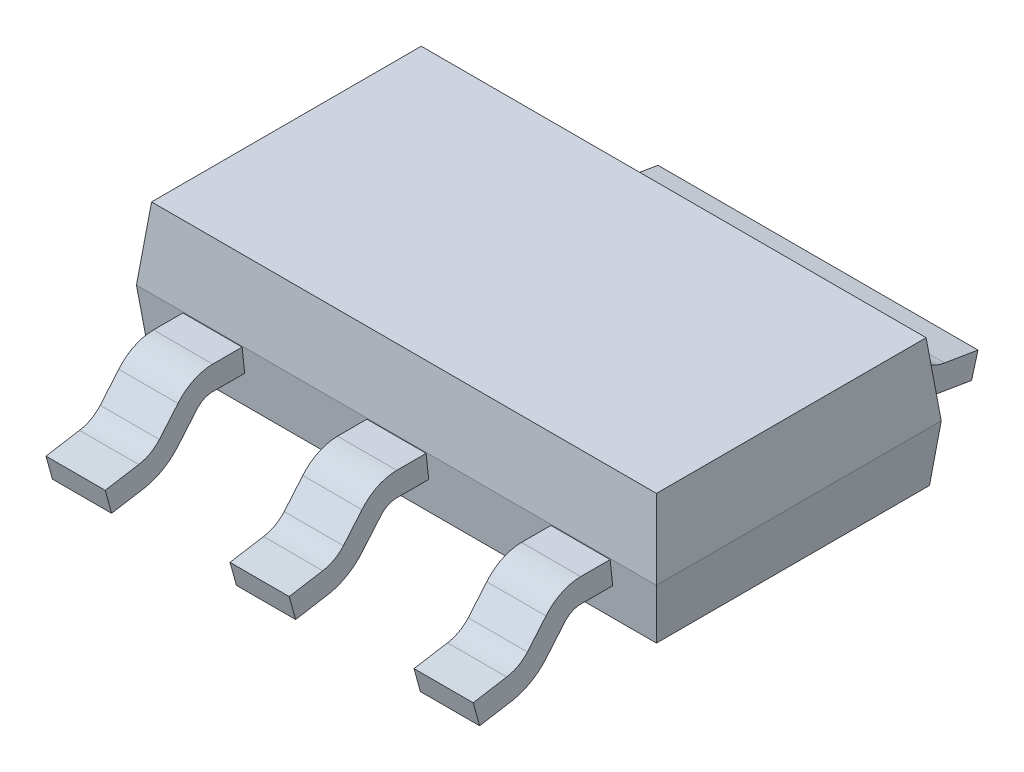
SolidWorks part; units mm, degrees
ref_plane "Plano frontal" through (0, 0, 0) normal (0, 0, 1) x (1, 0, 0)
ref_plane "Plano superior" through (0, 0, 0) normal (0, 1, 0) x (1, 0, 0)
ref_plane "Plano direito" through (0, 0, 0) normal (1, 0, 0) x (0, 0, -1)
sketch "Esboço1" plane through (0, 0, 0) normal (0, 1, 0) x (1, 0, 0)
  line L1 (-3.25, 1.78) -> (3.25, 1.78)
  line L2 (-3.25, 1.78) -> (-3.25, -1.78)
  line L3 (-3.25, -1.78) -> (3.25, -1.78)
  line L4 (3.25, 1.78) -> (3.25, -1.78)
  dimension "D1" = 3.25
  dimension "D2" = 6.5
  dimension "D3" = 1.78
  dimension "D4" = 3.56
extrude "Extrusão1" add sketch "Esboço1" along normal blind 0.9 draft 6 and the other way blind 0.7 draft 6
sketch "Esboço2" plane through (0, 0, 0) normal (1, 0, 0) x (0, 0, -1)
  line L0 (-1.7711, -0.0848) -> (-2.1389, -0.0848)
  line L1 (-1.7064, -0.7) -> (-1.78, 0) construction
  line L2 (-2.5209, -0.2622) -> (-2.7525, -0.5365)
  line L3 (-3.0523, -0.707) -> (-3.4711, -0.7768)
  arc A0 (-2.1389, -0.0848) -> (-2.5209, -0.2622) centre (-2.1389, -0.5848) ccw
  arc A1 (-2.7525, -0.5365) -> (-3.0523, -0.707) centre (-3.1345, -0.2138) cw
  point P8 (-2.3711, -0.0848)
  point P11 (-2.8711, -0.6768)
  dimension "D5" = 0.5
  dimension "D1" = 0.6
  dimension "D2" = 0.6
  dimension "D3" = 0.5
  dimension "D4" = 0.1
  dimension "D6" = 0.692
sketch "Esboço3" plane through (0, -0.185, 1.7606) normal (0, -0.1045, 0.9945) x (1, 0, 0)
  line L0 (0, 0.0028) -> (0, 0.142) construction
  line L1 (-0.37, 0.1733) -> (0.37, 0.1733)
  line L2 (-0.37, 0.1733) -> (-0.37, -0.1267)
  line L3 (-0.37, -0.1267) -> (0.37, -0.1267)
  line L4 (0.37, 0.1733) -> (0.37, -0.1267)
  dimension "D1" = 0.74
  dimension "D2" = 0.37
  dimension "D3" = 0.3
sweep "Varredura1" add profiles "Esboço3" path "Esboço2"
pattern_linear "Padrão linear1" count 2 spacing 2.3 along (1, 0, 0) count 2 spacing 2.3 along (-1, 0, 0) of "Varredura1"
sketch "Esboço4" plane through (0, 0, 0) normal (1, 0, 0) x (0, 0, -1)
  line L0 (1.7703, -0.092) -> (2.1387, -0.092)
  line L1 (1.7064, -0.7) -> (1.78, 0) construction
  line L2 (2.5201, -0.2687) -> (2.7519, -0.5421)
  line L3 (3.0511, -0.7121) -> (3.4703, -0.782)
  arc A0 (2.1387, -0.092) -> (2.5201, -0.2687) centre (2.1387, -0.592) cw
  arc A1 (2.7519, -0.5421) -> (3.0511, -0.7121) centre (3.1333, -0.2189) ccw
  point P8 (2.3703, -0.092)
  point P11 (2.8703, -0.682)
  dimension "D6" = 0.5
  dimension "D1" = 0.6
  dimension "D2" = 0.5
  dimension "D3" = 0.6
  dimension "D4" = 0.1
  dimension "D5" = 0.59
sketch "Esboço5" plane through (0, -0.185, -1.7606) normal (0, -0.1045, -0.9945) x (-1, 0, 0)
  line L0 (0, -0.0038) -> (0, -0.2515) construction
  line L1 (-2, 0.1648) -> (2, 0.1648)
  line L2 (-2, 0.1648) -> (-2, -0.1352)
  line L3 (-2, -0.1352) -> (2, -0.1352)
  line L4 (2, 0.1648) -> (2, -0.1352)
  dimension "D1" = 0.3
  dimension "D2" = 4
  dimension "D3" = 2
sweep "Varredura2" add profiles "Esboço5" path "Esboço4"
